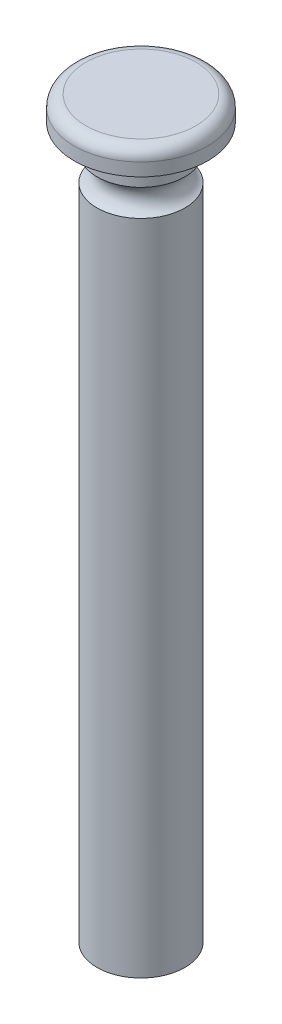
SolidWorks part; units mm, degrees
ref_plane "Front Plane" through (0, 0, 0) normal (0, 0, 1) x (1, 0, 0)
ref_plane "Top Plane" through (0, 0, 0) normal (0, 1, 0) x (1, 0, 0)
ref_plane "Right Plane" through (0, 0, 0) normal (1, 0, 0) x (0, 0, -1)
sketch "Sketch2" plane through (0, 0, 0) normal (0, 1, 0) x (1, 0, 0)
  circle A0 centre (0, 0) radius 9.525
extrude "Extrude1" add sketch "Sketch2" along normal blind 153.924
sketch "Sketch3" plane through (0, 153.924, 0) normal (0, 1, 0) x (-1, 0, 0)
  circle A0 centre (0, 0) radius 14.478
extrude "Extrude2" add sketch "Sketch3" along normal blind 5.334
sketch "Sketch14" plane through (0, 0, 0) normal (0, 0, 1) x (1, 0, 0)
  line L0 (9.525, 153.924) -> (9.525, 145.542) construction
  line L1 (9.525, 0) -> (9.525, 153.924) construction
  line L2 (9.525, 145.542) -> (8.128, 145.542) construction
  line L3 (9.525, 145.542) -> (9.525, 142.621) construction
  line L4 (9.525, 148.463) -> (9.525, 142.621)
  line L5 (9.525, 145.542) -> (9.525, 148.463) construction
  line L6 (9.525, 145.542) -> (-9.525, 145.542) construction
  line L8 (0, 145.542) -> (0, 153.924) construction
  line L9 (-9.525, 153.924) -> (9.525, 153.924) construction
  line L10 (-9.525, 153.924) -> (-9.525, 0) construction
  arc A0 (9.525, 142.621) -> (9.525, 148.463) centre (10.7961, 145.542) cw
revolve "Cut-Revolve1" cut sketch "Sketch14" angle 360 about L8
fillet "Fillet1" radius 2.54 1 edges at (0, 159.258, 14.478)
